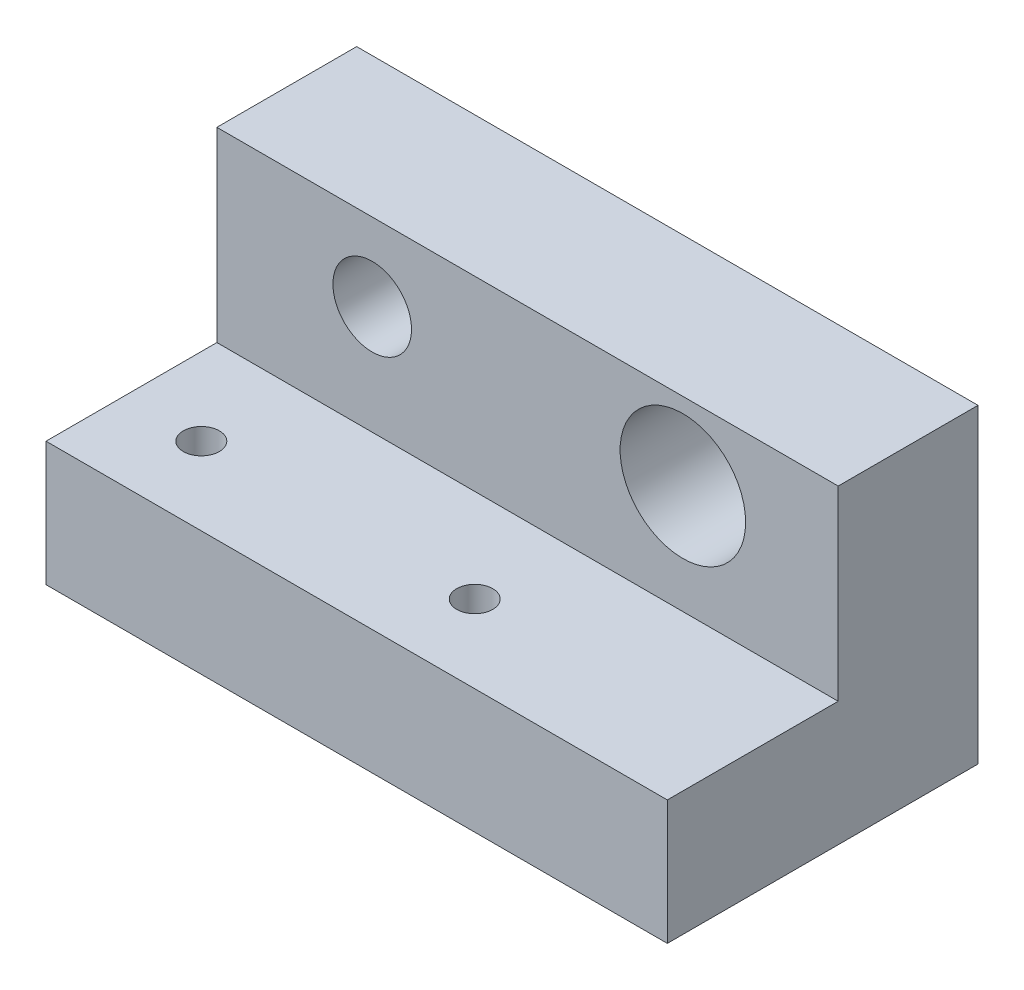
SolidWorks part; units mm, degrees
material "Delrin 2700 NC010, Low Viscosity Acetal Copolymer (SS)"
ref_plane "Front Plane" through (0, 0, 0) normal (0, 0, 1) x (1, 0, 0)
ref_plane "Top Plane" through (0, 0, 0) normal (0, 1, 0) x (1, 0, 0)
ref_plane "Right Plane" through (0, 0, 0) normal (1, 0, 0) x (0, 0, -1)
sketch "Sketch3" plane through (0, 0, 0) normal (1, 0, 0) x (0, 0, -1)
  line L0 (0, 0) -> (25.4, 0)
  line L1 (25.4, 0) -> (25.4, 25.4)
  line L2 (25.4, 25.4) -> (13.97, 25.4)
  line L3 (13.97, 25.4) -> (13.97, 10.16)
  line L4 (13.97, 10.16) -> (0, 10.16)
  line L5 (0, 10.16) -> (0, 0)
  dimension "D1" = 10.16
  dimension "D2" = 25.4
  dimension "D3" = 25.4
  dimension "D4" = 11.43
extrude "Boss-Extrude1" add sketch "Sketch3" against normal blind 50.8
sketch "Sketch4" plane through (0, 10.16, 0) normal (0, 1, 0) x (1, 0, 0)
  line L0 (-50.8, 25.4) -> (0, 25.4) construction
  line L1 (-50.8, 13.97) -> (-50.8, 0) construction
  line L2 (-50.8, 25.4) -> (-50.8, 13.97) construction
  circle A0 centre (-44.45, 6.35) radius 1.4732
  circle A1 centre (-22.098, 6.35) radius 1.4732
  dimension "D1" = 2.9464
  dimension "D2" = 19.05
  dimension "D3" = 6.35
  dimension "D4" = 28.702
extrude "Cut-Extrude1" cut sketch "Sketch4" against normal through all
sketch "Sketch5" plane through (0, 0, -13.97) normal (0, 0, 1) x (1, 0, 0)
  line L0 (-50.8, 25.4) -> (-50.8, 10.16) construction
  line L1 (-50.8, 0) -> (0, 0) construction
  circle A0 centre (-38.1, 19.05) radius 3.2131
  circle A1 centre (-12.7, 19.05) radius 5.1308
  dimension "D1" = 6.4262
  dimension "D5" = 10.2616
  dimension "D2" = 12.7
  dimension "D3" = 19.05
  dimension "D4" = 38.1
extrude "Cut-Extrude2" cut sketch "Sketch5" against normal blind 50.8
